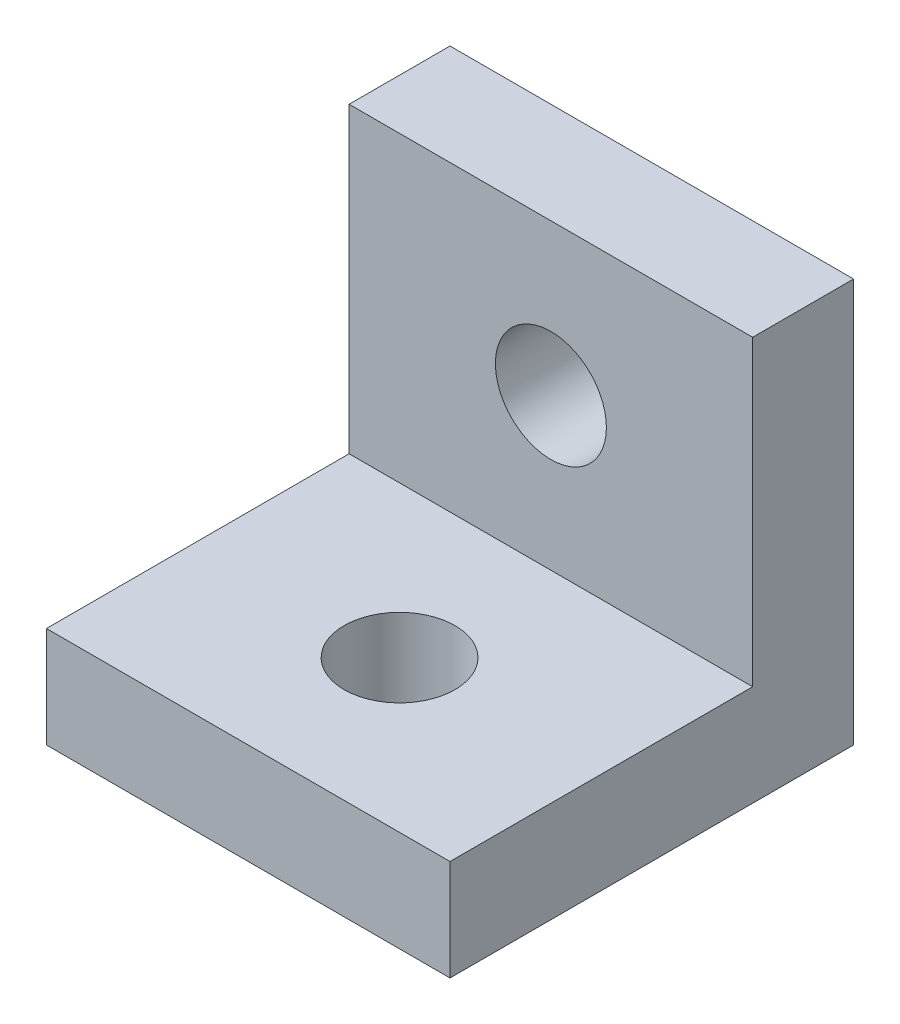
SolidWorks part; units mm, degrees
ref_plane "Front Plane" through (0, 0, 0) normal (0, 0, 1) x (1, 0, 0)
ref_plane "Top Plane" through (0, 0, 0) normal (0, 1, 0) x (1, 0, 0)
ref_plane "Right Plane" through (0, 0, 0) normal (1, 0, 0) x (0, 0, -1)
sketch "Sketch1" plane through (0, 0, 0) normal (0, 0, 1) x (1, 0, 0)
  line L1 (0, 0) -> (10.16, 0)
  line L2 (0, 0) -> (0, 10.16)
  line L3 (0, 10.16) -> (10.16, 10.16)
  line L4 (10.16, 0) -> (10.16, 10.16)
  dimension "D1" = 10.16
  dimension "D2" = 10.16
extrude "Boss-Extrude1" add sketch "Sketch1" along normal blind 2.54
sketch "Sketch2" plane through (0, 0, 2.54) normal (0, 0, 1) x (1, 0, 0)
  line L0 (10.16, 0) -> (10.16, 10.16) construction
  line L1 (0, 0) -> (10.16, 0)
  line L2 (0, 0) -> (0, 2.54)
  line L3 (0, 2.54) -> (10.16, 2.54)
  line L4 (10.16, 0) -> (10.16, 2.54)
  dimension "D1" = 2.54
extrude "Boss-Extrude2" add sketch "Sketch2" along normal blind 7.62
sketch "Sketch3" plane through (0, 0, 2.54) normal (0, 0, 1) x (1, 0, 0)
  circle A0 centre (5.08, 6.35) radius 1.397
  dimension "D3" = 2.794
  dimension "D1" = 6.35
  dimension "D2" = 5.08
extrude "Cut-Extrude1" cut sketch "Sketch3" against normal blind 10.16
sketch "Sketch4" plane through (0, 2.54, 0) normal (0, 1, 0) x (1, 0, 0)
  circle A0 centre (5.08, -6.35) radius 1.397
  point P2 (0, 0)
  point P6 (13.5369, 21.2408)
  dimension "D1" = 2.794
  dimension "D2" = 5.08
  dimension "D3" = 6.35
extrude "Cut-Extrude2" cut sketch "Sketch4" against normal blind 10.16
